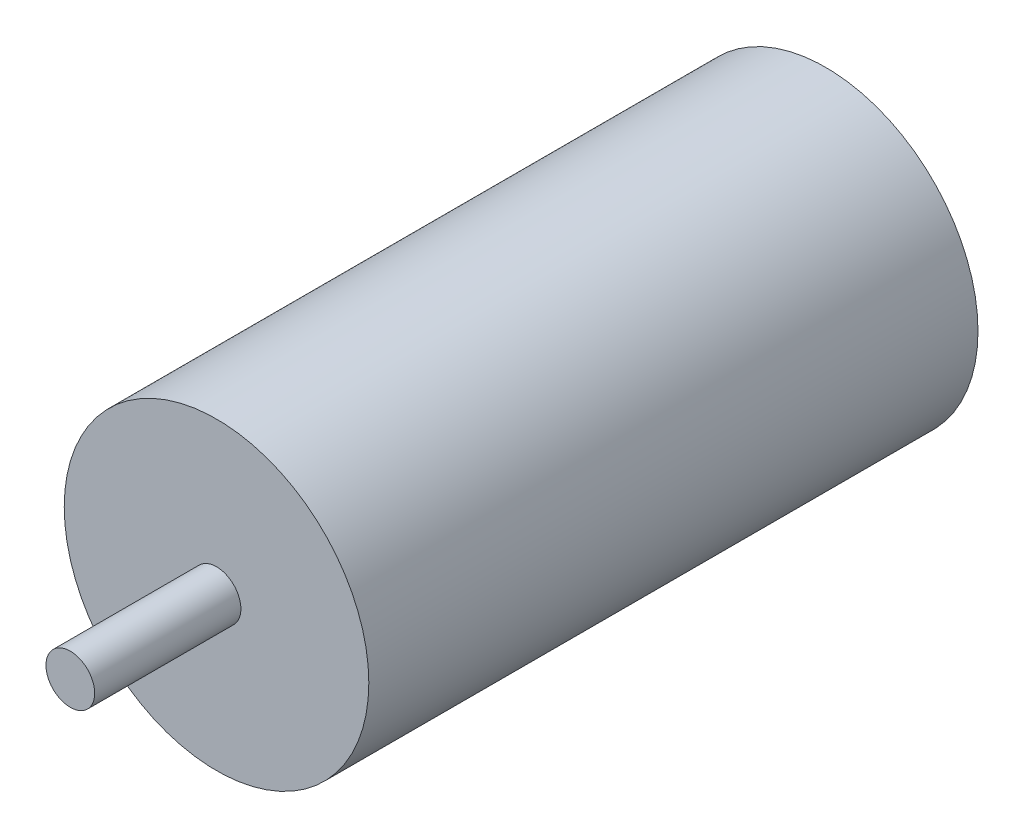
SolidWorks part; units mm, degrees
ref_plane "Front Plane" through (0, 0, 0) normal (0, 0, 1) x (1, 0, 0)
ref_plane "Top Plane" through (0, 0, 0) normal (0, 1, 0) x (1, 0, 0)
ref_plane "Right Plane" through (0, 0, 0) normal (1, 0, 0) x (0, 0, -1)
sketch "Sketch1" plane through (0, 0, 0) normal (0, 0, 1) x (1, 0, 0)
  circle A0 centre (0, 0) radius 12.5
  dimension "D1" = 25
extrude "Boss-Extrude1" add sketch "Sketch1" along normal blind 50
sketch "Sketch2" plane through (0, 0, 50) normal (0, 0, 1) x (1, 0, 0)
  circle A0 centre (0, 0) radius 2
  dimension "D1" = 4
extrude "Boss-Extrude2" add sketch "Sketch2" along normal blind 12
